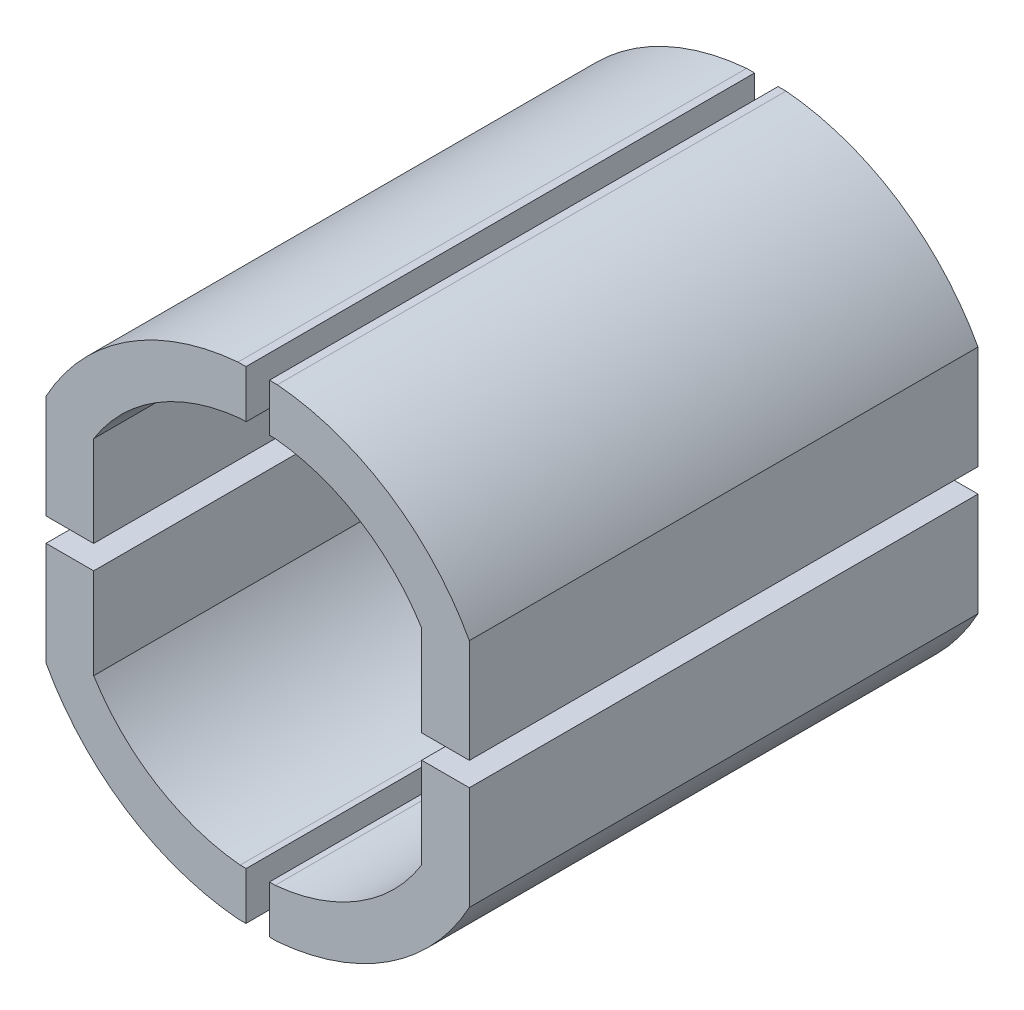
SolidWorks part; units mm, degrees
ref_plane "Front Plane" through (0, 0, 0) normal (0, 0, 1) x (1, 0, 0)
ref_plane "Top Plane" through (0, 0, 0) normal (0, 1, 0) x (1, 0, 0)
ref_plane "Right Plane" through (0, 0, 0) normal (1, 0, 0) x (0, 0, -1)
sketch "Sketch1" plane through (0, 0, 0) normal (0, 0, 1) x (1, 0, 0)
  line L0 (11.0555, 15.9152) -> (11.0555, 21.6277)
  line L5 (1.8422, 27.3387) -> (1.4789, 27.3387)
  line L8 (0, 0) -> (0.0123, 3)
  line L9 (-0.3644, 3) -> (0.0123, 3)
  line L10 (0, 30.3387) -> (0.0123, 27.3387)
  line L11 (-0.3644, 27.3387) -> (0.0123, 27.3387)
  line L122 (-12.5777, 22.4344) -> (-12.5777, 15.9152)
  line L123 (1.9778, 30.3387) -> (1.4789, 30.3387)
  line L124 (14.0555, 7.9043) -> (14.0555, 14.4234)
  line L125 (-0.5, 0) -> (0, 0)
  line L143 (1.4789, 27.3387) -> (1.4789, 30.3387)
  line L153 (-12.5777, 14.4234) -> (-9.5777, 14.4234)
  line L154 (-9.5777, 15.9152) -> (-12.5777, 15.9152)
  line L170 (1.4789, 0) -> (1.4789, 3)
  line L182 (14.0555, 15.9152) -> (14.0555, 22.4344)
  line L183 (0, 30.3387) -> (-0.5, 30.3387)
  line L184 (-12.5777, 14.4234) -> (-12.5777, 7.9043)
  line L186 (11.0555, 14.4234) -> (14.0555, 14.4234)
  line L187 (14.0555, 15.9152) -> (11.0555, 15.9152)
  line L188 (1.4789, 0) -> (1.9778, 0)
  line L190 (-9.5777, 21.6277) -> (-9.5777, 15.9152)
  line L191 (-9.5777, 14.4234) -> (-9.5777, 8.711)
  line L193 (1.4789, 3) -> (1.8422, 3)
  line L194 (11.0555, 8.711) -> (11.0555, 14.4234)
  line L195 (-0.3644, 3) -> (0, 3) construction
  line L196 (0, 27.3387) -> (-0.3644, 27.3387) construction
  arc A0 (11.0555, 21.6277) -> (1.8422, 27.3387) centre (0.6756, 15.1695) ccw
  arc A108 (-0.5, 30.3387) -> (-12.5777, 22.4344) centre (0.8022, 15.1695) ccw
  arc A109 (14.0555, 22.4344) -> (1.9778, 30.3387) centre (0.6756, 15.1695) ccw
  arc A110 (1.9778, 0) -> (14.0555, 7.9043) centre (0.6756, 15.1692) ccw
  arc A111 (-12.5777, 7.9043) -> (-0.5, 0) centre (0.8022, 15.1692) ccw
  arc A143 (-0.3644, 27.3387) -> (-9.5777, 21.6277) centre (0.8022, 15.1695) ccw
  arc A144 (-9.5777, 8.711) -> (-0.3644, 3) centre (0.8022, 15.1692) ccw
  arc A147 (1.8422, 3) -> (11.0555, 8.711) centre (0.6756, 15.1692) ccw
  dimension "D1" = 3
  dimension "D2" = 3
  dimension "D3" = 3
  dimension "D4" = 3
extrude "Boss-Extrude1" add sketch "Sketch1" along normal up to surface (32 mm away) contours L10 L11 A143 L190 L154 L122 A108 L183 | L8 L9 A144 L191 L153 L184 A111 L125 | L170 L193 A147 L194 L186 L124 A110 L188 | L182 A109 L123 L143 L5 A0 L0 L187
